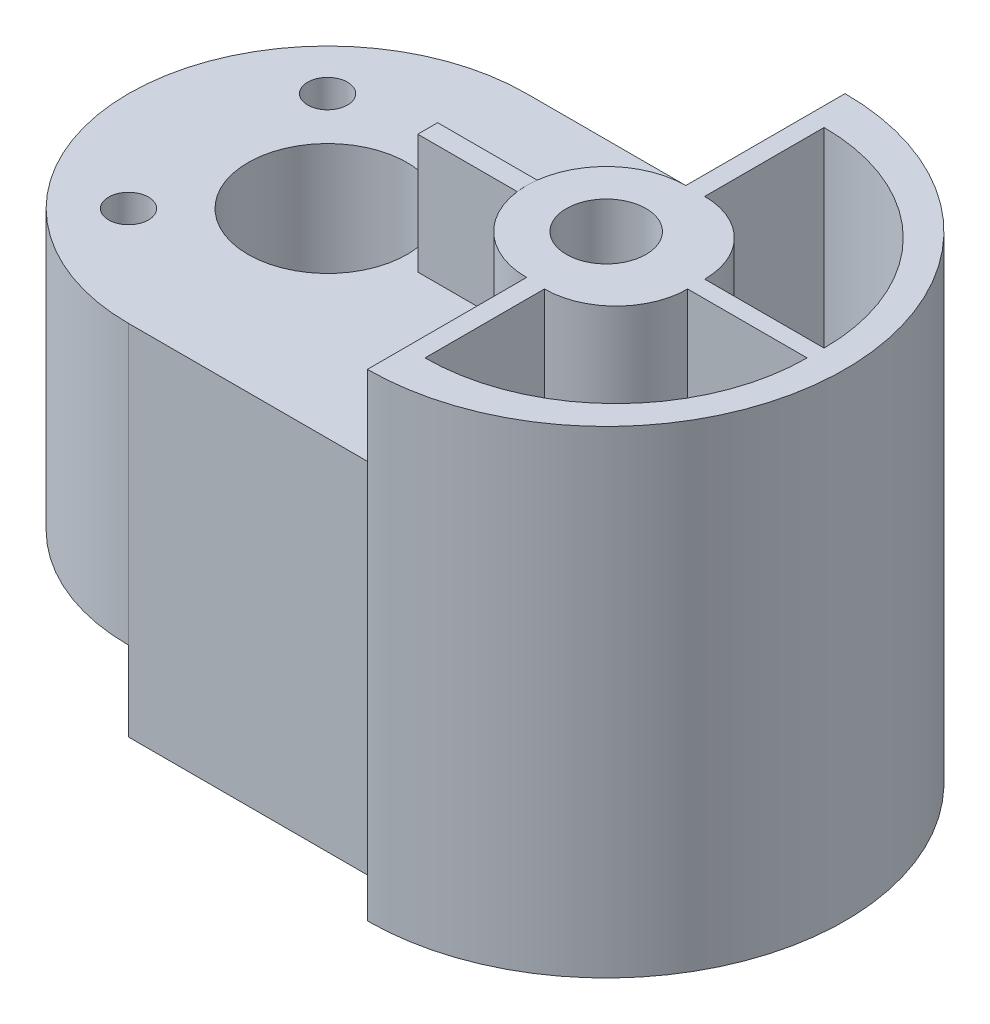
SolidWorks part; units mm, degrees
ref_plane "Front Plane" through (0, 0, 0) normal (0, 0, 1) x (1, 0, 0)
ref_plane "Top Plane" through (0, 0, 0) normal (0, 1, 0) x (1, 0, 0)
ref_plane "Right Plane" through (0, 0, 0) normal (1, 0, 0) x (0, 0, -1)
sketch "Sketch1" plane through (0, 0, 0) normal (0, 1, 0) x (1, 0, 0)
  line L1 (0, 0) -> (180, 0)
  line L2 (0, 0) -> (0, 120)
  line L3 (0, 120) -> (180, 120)
  line L4 (180, 0) -> (180, 120)
  dimension "D1" = 180
  dimension "D2" = 120
extrude "Boss-Extrude2" add sketch "Sketch1" along normal blind 120
sketch "Sketch2" plane through (0, 0, 0) normal (0, 1, 0) x (1, 0, 0)
  line L1 (0, 120) -> (110, 120)
  line L2 (0, 120) -> (0, 110)
  line L3 (0, 110) -> (110, 110)
  line L4 (110, 120) -> (110, 110)
  line L5 (0, 0) -> (110, 0)
  line L6 (0, 0) -> (0, 10)
  line L7 (0, 10) -> (110, 10)
  line L8 (110, 0) -> (110, 10)
  dimension "D1" = 10
  dimension "D2" = 70
  dimension "D3" = 10
  dimension "D4" = 70
extrude "Cut-Extrude1" cut sketch "Sketch2" along normal blind 120
sketch "Sketch3" plane through (0, 120, 0) normal (0, 1, 0) x (1, 0, 0)
  line L0 (180, 120) -> (110, 120) construction
  line L1 (110, 110) -> (110, 120)
  line L2 (110, 120) -> (120, 120)
  line L3 (110, 0) -> (180, 0) construction
  line L4 (120, 0) -> (110, 0)
  line L5 (110, 0) -> (110, 10)
  arc A0 (110, 110) -> (120, 120) centre (110, 120) ccw
  arc A1 (110, 10) -> (120, 0) centre (110, 0) cw
extrude "Cut-Extrude2" cut sketch "Sketch3" against normal blind 120
sketch "Sketch4" plane through (0, 120, 0) normal (0, 1, 0) x (1, 0, 0)
  line L0 (180, 120) -> (120, 120) construction
  line L1 (120, 120) -> (180, 120)
  line L2 (180, 120) -> (180, 0)
  line L3 (180, 0) -> (120, 0)
  line L4 (120, 0) -> (180, 0)
  arc A0 (120, 120) -> (120, 0) centre (120, 60) cw
  line M3 (120, 0) -> (180, 0)
  line M4 (180, 0) -> (180, 120)
  line M5 (180, 120) -> (120, 120)
  dimension "D3" = 60
  dimension "D1" = 60
  dimension "D2" = 0
  dimension "D4" = 60
  dimension "D5" = 60
  dimension "D6" = 120
extrude "Cut-Extrude3" cut sketch "Sketch4" against normal blind 120 contours A0 L2 M5 | A0 M4 M3
sketch "Sketch5" plane through (0, 120, 0) normal (0, 1, 0) x (1, 0, 0)
  line L0 (0, 110) -> (110, 110) construction
  line L1 (50, 110) -> (0, 110)
  line L2 (0, 110) -> (0, 10)
  line L3 (0, 10) -> (50, 10)
  arc A0 (50, 110) -> (50, 10) centre (50, 60) ccw
  line M4 (110, 110) -> (0, 110)
  line M5 (0, 110) -> (0, 10)
  line M6 (0, 10) -> (110, 10)
  dimension "D1" = 50
  dimension "D2" = 50
  dimension "D3" = 50
  dimension "D4" = 50
extrude "Cut-Extrude4" cut sketch "Sketch5" against normal blind 120 contours A0 M4 M5 | A0 L2 M6
sketch "Sketch6" plane through (0, 120, 0) normal (0, 1, 0) x (1, 0, 0)
  circle A0 centre (25, 85) radius 5
  circle A1 centre (25, 35) radius 5
  dimension "D1" = 10
  dimension "D2" = 10
  dimension "D3" = 25
  dimension "D4" = 25
  dimension "D5" = 25
  dimension "D6" = 25
extrude "Cut-Extrude5" cut sketch "Sketch6" against normal blind 120
sketch "Sketch7" plane through (0, 120, 0) normal (0, 1, 0) x (1, 0, 0)
  circle A0 centre (120, 60) radius 10
  dimension "D1" = 20
extrude "Cut-Extrude6" cut sketch "Sketch7" against normal blind 120
sketch "Sketch9" plane through (0, 120, 0) normal (0, 1, 0) x (1, 0, 0)
  line L0 (120, 120) -> (120, 0)
  line L1 (110, 110) -> (50, 110)
  line L2 (50, 10) -> (110, 10)
  arc A0 (50, 110) -> (50, 10) centre (50, 60) ccw
  arc A1 (120, 120) -> (110, 110) centre (110, 120) cw
  arc A2 (110, 110) -> (120, 120) centre (110, 120) ccw construction
  arc A3 (110, 10) -> (120, 0) centre (110, 0) cw
  arc A4 (120, 0) -> (110, 10) centre (110, 0) ccw construction
extrude "Cut-Extrude7" cut sketch "Sketch9" against normal blind 30
sketch "Sketch10" plane through (0, 90, 0) normal (0, 1, 0) x (1, 0, 0)
  line L0 (120, 70) -> (120, 120) construction
  line L1 (120, 0) -> (120, 50) construction
  line L2 (120, 70) -> (120, 80)
  line L3 (120, 50) -> (120, 40)
  arc A0 (120, 80) -> (120, 40) centre (120, 60) ccw
  arc A1 (120, 70) -> (120, 50) centre (120, 60) ccw construction
  arc A2 (120, 70) -> (120, 50) centre (120, 60) ccw
  dimension "D1" = 20
extrude "Boss-Extrude3" add sketch "Sketch10" along normal blind 30
sketch "Sketch11" plane through (0, 120, 0) normal (0, 1, 0) x (1, 0, 0)
  line L0 (124.7431, 80) -> (124.7431, 110)
  line L1 (120, 80) -> (120, 120) construction
  line L2 (142.7431, 62) -> (172.7431, 62)
  arc A0 (124.7431, 80) -> (142.7431, 62) centre (124.7431, 62) cw
  circle A1 centre (120, 60) radius 10 construction
  arc A2 (124.7431, 110) -> (172.7431, 62) centre (124.7431, 62) cw
  point P5 (110.202, 62)
  point P6 (120, 100)
  dimension "D3" = 18
  dimension "D1" = 18
  dimension "D2" = 0
  dimension "D4" = 18
  dimension "D5" = 40
  dimension "D6" = 32.5411
  dimension "D7" = 14.5411
  dimension "D8" = 62
  dimension "D9" = 30
  dimension "D10" = 4.7431
extrude "Cut-Extrude8" cut sketch "Sketch11" against normal blind 60
sketch "Sketch12" plane through (0, 120, 0) normal (0, 1, 0) x (1, 0, 0)
  line L0 (124.7431, 39.7227) -> (124.7431, 9.7227)
  line L1 (120, 0) -> (120, 40) construction
  line L3 (142.7431, 57.7227) -> (172.7431, 57.7227)
  arc A0 (142.7431, 57.7227) -> (124.7431, 39.7227) centre (124.7431, 57.7227) cw
  arc A1 (124.7431, 9.7227) -> (172.7431, 57.7227) centre (124.7431, 57.7227) ccw
  circle A2 centre (120, 60) radius 10 construction
  point P3 (110.2628, 57.7227)
  dimension "D4" = 18
  dimension "D1" = 18
  dimension "D2" = 18
  dimension "D3" = 0
  dimension "D5" = 39.7227
  dimension "D6" = 30
  dimension "D7" = 4.7431
extrude "Cut-Extrude9" cut sketch "Sketch12" against normal blind 60
sketch "Sketch13" plane through (0, 60, 0) normal (0, 1, 0) x (1, 0, 0)
  line L0 (142.7431, 62) -> (172.7431, 62) construction
  line L1 (124.7431, 80) -> (124.7431, 100)
  line L2 (124.7431, 110) -> (124.7431, 80) construction
  line L3 (142.7431, 62) -> (162.7431, 62)
  arc A0 (124.7431, 80) -> (142.7431, 62) centre (124.7431, 62) cw
  arc A1 (142.7431, 62) -> (124.7431, 80) centre (124.7431, 62) ccw construction
  arc A2 (124.7431, 100) -> (162.7431, 62) centre (124.7431, 62) cw
  dimension "D1" = 20
  dimension "D2" = 10
extrude "Cut-Extrude10" cut sketch "Sketch13" against normal blind 60
sketch "Sketch14" plane through (0, 60, 0) normal (0, 1, 0) x (1, 0, 0)
  line L0 (124.7431, 39.7227) -> (124.7431, 9.7227) construction
  line L1 (124.7431, 39.7227) -> (124.7431, 19.7227)
  line L2 (142.7431, 57.7227) -> (162.7431, 57.7227)
  arc A0 (142.7431, 57.7227) -> (124.7431, 39.7227) centre (124.7431, 57.7227) cw
  arc A1 (124.7431, 19.7227) -> (162.7431, 57.7227) centre (124.7431, 57.7227) ccw
  dimension "D1" = 20
extrude "Cut-Extrude11" cut sketch "Sketch14" against normal blind 60
sketch "Sketch15" plane through (0, 90, 0) normal (0, 1, 0) x (1, 0, 0)
  line L0 (50, 10) -> (110, 10) construction
  line L1 (100.1569, 62.5) -> (75.1569, 62.5)
  line L2 (100.1569, 62.5) -> (100.1569, 57.5)
  line L3 (100.1569, 57.5) -> (75.1569, 57.5)
  line L4 (75.1569, 62.5) -> (75.1569, 57.5)
  line L5 (110, 110) -> (50, 110) construction
  arc A0 (120, 80) -> (120, 40) centre (120, 60) ccw construction
  dimension "D1" = 5
  dimension "D2" = 47.5
  dimension "D3" = 47.5
  dimension "D4" = 25
extrude "Boss-Extrude5" add sketch "Sketch15" along normal blind 29.999
sketch "Sketch16" plane through (0, 90, 0) normal (0, 1, 0) x (1, 0, 0)
  circle A0 centre (50, 60) radius 10
  dimension "D1" = 20
extrude "Cut-Extrude12" cut sketch "Sketch16" against normal blind 125.999
sketch "Sketch17" plane through (0, 90, 0) normal (0, 1, 0) x (1, 0, 0)
  circle A0 centre (50, 60) radius 10
  circle A1 centre (50, 60) radius 20
  dimension "D1" = 20
  dimension "D2" = 40
extrude "Cut-Extrude13" cut sketch "Sketch17" against normal blind 30
ref_plane "Plane1" through (120, 120, -40) normal (1, 0, 0) x (0, 0, -1)
sketch "Sketch19" plane through (0, 0, 0) normal (0, -1, 0) x (-1, 0, 0)
  line L0 (-50, 110) -> (-50, 10)
  arc A0 (-50, 110) -> (-50, 10) centre (-50, 60) cw
  arc A1 (-50, 70) -> (-50, 50) centre (-50, 60) cw
  circle A2 centre (-50, 60) radius 10 construction
  circle M1 centre (-50, 60) radius 10
  circle M11 centre (-25, 35) radius 5
  circle M12 centre (-25, 85) radius 5
  arc M14 (-50, 10) -> (-50, 110) centre (-50, 60) ccw
extrude "Cut-Extrude14" cut sketch "Sketch19" against normal blind 20 contours L0 M14 M1 M11 M12
sketch "Sketch20" plane through (0, 60, 0) normal (0, 1, 0) x (1, 0, 0)
  circle A0 centre (50, 60) radius 10
  circle A1 centre (50, 60) radius 20
  dimension "D1" = 20
  dimension "D2" = 40
extrude "Cut-Extrude15" cut sketch "Sketch20" against normal blind 84.462
sketch "Sketch21" plane through (0, 20, 0) normal (0, -1, 0) x (1, 0, 0)
  line L0 (50, -40) -> (50, -10) construction
  line L1 (50, -70) -> (50, -80)
  line L2 (50, -50) -> (50, -40)
  arc A0 (50, -80) -> (50, -40) centre (50, -60) cw
  arc A1 (50, -70) -> (50, -50) centre (50, -60) cw
  dimension "D1" = 10
extrude "Boss-Extrude6" add sketch "Sketch21" against normal blind 20
sketch "Sketch22" plane through (0, 20, 0) normal (0, -1, 0) x (1, 0, 0)
  line L0 (50, -50) -> (50, -40) construction
  line L1 (50, -40) -> (50, -10) construction
  line L2 (50, -70) -> (50, -80)
  line L3 (50, -50) -> (50, -40)
  arc A0 (50, -70) -> (50, -50) centre (50, -60) ccw
  arc A1 (50, -80) -> (50, -40) centre (50, -60) ccw
extrude "Boss-Extrude7" add sketch "Sketch22" against normal blind 20
